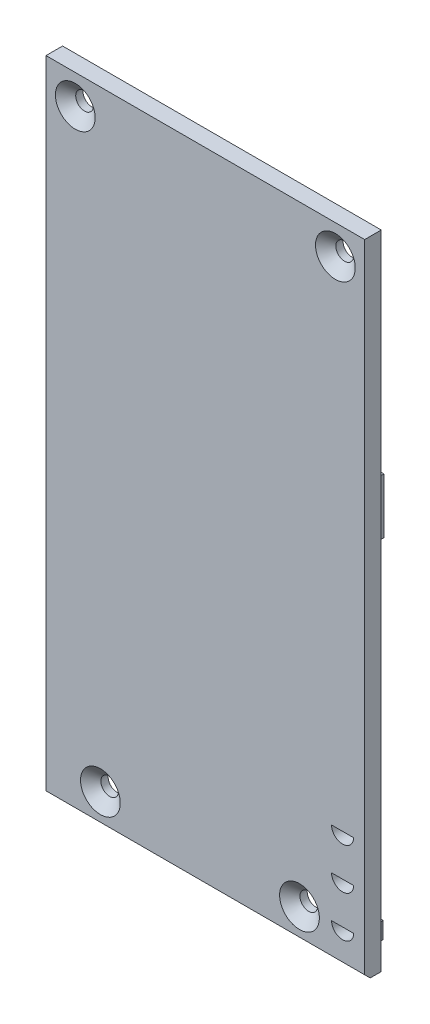
SolidWorks part; units mm, degrees
ref_plane "Front Plane" through (0, 0, 0) normal (0, 0, 1) x (1, 0, 0)
ref_plane "Top Plane" through (0, 0, 0) normal (0, 1, 0) x (1, 0, 0)
ref_plane "Right Plane" through (0, 0, 0) normal (1, 0, 0) x (0, 0, -1)
sketch "Sketch1" plane through (0, 0, 0) normal (0, 0, 1) x (1, 0, 0)
  line L1 (0, 0) -> (57.7, 0)
  line L2 (0, 0) -> (0, 114.7)
  line L3 (0, 114.7) -> (57.7, 114.7)
  line L4 (57.7, 0) -> (57.7, 114.7)
  dimension "D1" = 114.7
  dimension "D2" = 57.7
extrude "Boss-Extrude1" add sketch "Sketch1" along normal blind 3
sketch "Sketch2" plane through (0, 0, 3) normal (0, 0, 1) x (1, 0, 0)
  line L1 (0, 114.7) -> (0, 0) construction
  line L2 (57.7, 114.7) -> (0, 114.7) construction
  line L3 (57.7, 0) -> (57.7, 114.7) construction
  line L4 (0, 0) -> (57.7, 0) construction
  circle A0 centre (5.3, 109.4) radius 1.6
  circle A1 centre (52.4, 109.4) radius 1.6
  circle A2 centre (9.85, 4.2) radius 1.6
  circle A3 centre (45.9, 4.2) radius 1.6
  dimension "D1" = 3.2
  dimension "D2" = 5.3
  dimension "D3" = 5.3
  dimension "D4" = 5.3
  dimension "D5" = 5.3
  dimension "D6" = 9.85
  dimension "D7" = 11.8
  dimension "D8" = 4.2
  dimension "D9" = 4.2
extrude "Cut-Extrude1" cut sketch "Sketch2" against normal blind 3
chamfer "Chamfer1" distance 2 angle 40 4 edges at (11.45, 4.2, 3) (54, 109.4, 3) (6.9, 109.4, 3) (47.5, 4.2, 3)
sketch "Sketch4" plane through (0, 0, 0) normal (0, -1, 0) x (1, 0, 0)
  line L1 (0, 3) -> (57.7, 3)
  line L2 (0, 3) -> (0, 0)
  line L3 (0, 0) -> (57.7, 0)
  line L4 (57.7, 3) -> (57.7, 0)
extrude "Boss-Extrude2" add sketch "Sketch4" along normal blind 1.6
sketch "Sketch5" plane through (0, 0, 0) normal (0, 0, -1) x (-1, 0, 0)
  line L1 (-45.7, 105.2) -> (-26.7, 105.2)
  line L2 (-45.7, 105.2) -> (-45.7, 99.2)
  line L3 (-45.7, 99.2) -> (-26.7, 99.2)
  line L4 (-26.7, 105.2) -> (-26.7, 99.2)
  line L5 (-57.7, 114.7) -> (0, 114.7) construction
  line L6 (-57.7, -1.6) -> (-57.7, 114.7) construction
  line L7 (0, 114.7) -> (0, -1.6) construction
  dimension "D1" = 6
  dimension "D2" = 12
  dimension "D3" = 26.7
  dimension "D4" = 9.5
extrude "Boss-Extrude3" add sketch "Sketch5" along normal blind 2.2
sketch "Sketch7" plane through (0, 0, 0) normal (0, 0, -1) x (-1, 0, 0)
  line L0 (-45.7, 105.2) -> (-45.7, 99.2) construction
  line L1 (-45.7, 104.2) -> (-26.7, 104.2)
  line L2 (-45.7, 104.2) -> (-45.7, 107.2)
  line L3 (-45.7, 107.2) -> (-26.7, 107.2)
  line L4 (-26.7, 104.2) -> (-26.7, 107.2)
  line L5 (-57.7, 114.7) -> (0, 114.7) construction
  dimension "D1" = 3
  dimension "D2" = 7.5
extrude "Boss-Extrude4" add sketch "Sketch7" along normal blind 4.5
chamfer "Chamfer2" distance 0.5 angle 45 1 edges at (36.2, 104.2, -4.5)
sketch "Sketch8" plane through (0, 0, 0) normal (0, 0, -1) x (-1, 0, 0)
  line L0 (0, -1.6) -> (-57.7, -1.6) construction
  line L1 (-39.7, 29.4) -> (-14, 29.4)
  line L2 (-39.7, 29.4) -> (-39.7, 26.4)
  line L3 (-39.7, 26.4) -> (-14, 26.4)
  line L4 (-14, 29.4) -> (-14, 26.4)
  line L5 (0, 114.7) -> (0, -1.6) construction
  line L6 (-57.7, -1.6) -> (-57.7, 114.7) construction
  line L8 (-54.7, 31.4) -> (-29.7, 31.4)
  line L9 (-54.7, 31.4) -> (-54.7, 35.4)
  line L10 (-54.7, 35.4) -> (-29.7, 35.4)
  line L11 (-29.7, 31.4) -> (-29.7, 35.4)
  dimension "D1" = 3
  dimension "D2" = 28
  dimension "D3" = 14
  dimension "D4" = 18
  dimension "D5" = 4
  dimension "D6" = 2
  dimension "D7" = 3
  dimension "D8" = 25
extrude "Boss-Extrude5" add sketch "Sketch8" along normal blind 2
sketch "Sketch9" plane through (0, 0, 0) normal (0, 0, -1) x (-1, 0, 0)
  line L0 (-57.7, -1.6) -> (-57.7, 114.7) construction
  line L1 (-39.7, 17.4) -> (-14, 17.4)
  line L2 (-39.7, 17.4) -> (-39.7, 10.4)
  line L3 (-39.7, 10.4) -> (-14, 10.4)
  line L4 (-14, 17.4) -> (-14, 10.4)
  line L5 (0, 114.7) -> (0, -1.6) construction
  line L7 (0, -1.6) -> (-57.7, -1.6) construction
  dimension "D1" = 7
  dimension "D2" = 18
  dimension "D3" = 14
  dimension "D4" = 19
extrude "Boss-Extrude6" add sketch "Sketch9" along normal blind 4.5
sketch "Sketch10" plane through (0, 0, 3) normal (0, 0, 1) x (1, 0, 0)
  line L0 (53.7, -1.6) -> (53.7, 25.8665) construction
  line L1 (57.7, -1.6) -> (0, -1.6) construction
  line L2 (57.7, -1.6) -> (57.7, 114.7) construction
  circle A0 centre (53.7, 19.9) radius 2
  circle A1 centre (53.7, 12.4) radius 2
  circle A2 centre (53.7, 4.9) radius 2
  point P10 (53.6857, 25.8665)
  dimension "D1" = 21.5
  dimension "D2" = 14
  dimension "D3" = 6.5
  dimension "D4" = 4
extrude "Cut-Extrude2" cut sketch "Sketch10" against normal blind 3
sketch "Sketch11" plane through (0, 0, 3) normal (0, 0, 1) x (1, 0, 0)
  line L1 (51.7, 19.9) -> (55.7, 19.9)
  line L2 (51.7, 19.9) -> (51.7, 21.9)
  line L3 (51.7, 21.9) -> (55.7, 21.9)
  line L4 (55.7, 19.9) -> (55.7, 21.9)
  line L5 (51.7, 12.4) -> (55.7, 12.4)
  line L6 (51.7, 12.4) -> (51.7, 14.4)
  line L7 (51.7, 14.4) -> (55.7, 14.4)
  line L8 (55.7, 12.4) -> (55.7, 14.4)
  line L9 (51.7, 4.9) -> (55.7, 4.9)
  line L10 (51.7, 4.9) -> (51.7, 6.9)
  line L11 (51.7, 6.9) -> (55.7, 6.9)
  line L12 (55.7, 4.9) -> (55.7, 6.9)
  circle A0 centre (53.7, 19.9) radius 2 construction
  circle A1 centre (53.7, 12.4) radius 2 construction
  circle A2 centre (53.7, 4.9) radius 2 construction
extrude "Boss-Extrude7" add sketch "Sketch11" against normal blind 0.7
sketch "Sketch12" plane through (0, 0, 0) normal (0, 0, -1) x (-1, 0, 0)
  line L1 (-55.7, 19.9) -> (-51.7, 19.9)
  line L2 (-55.7, 19.9) -> (-55.7, 17.9061)
  line L3 (-55.7, 17.9061) -> (-51.7, 17.9061)
  line L4 (-51.7, 19.9) -> (-51.7, 17.9061)
  line L5 (-55.7, 12.4) -> (-51.7, 12.4)
  line L6 (-55.7, 12.4) -> (-55.7, 10.4)
  line L7 (-55.7, 10.4) -> (-51.7, 10.4)
  line L8 (-51.7, 12.4) -> (-51.7, 10.4)
  line L9 (-55.7, 4.9) -> (-51.7, 4.9)
  line L10 (-55.7, 4.9) -> (-55.7, 2.9)
  line L11 (-55.7, 2.9) -> (-51.7, 2.9)
  line L12 (-51.7, 4.9) -> (-51.7, 2.9)
  circle A0 centre (-53.7, 12.4) radius 2 construction
extrude "Boss-Extrude11" add sketch "Sketch12" against normal blind 0.7
sketch "Sketch13" plane through (0, 0, 0) normal (0, 0, -1) x (-1, 0, 0)
  line L0 (0, 114.7) -> (0, -1.6) construction
  line L1 (-56.05, 1.6) -> (-51.55, 1.6)
  line L2 (-56.05, 1.6) -> (-56.05, 4.6)
  line L3 (-56.05, 4.6) -> (-51.55, 4.6)
  line L4 (-51.55, 1.6) -> (-51.55, 4.6)
  line L5 (-5, 1.6) -> (-2, 1.6)
  line L6 (-5, 1.6) -> (-5, 4.6)
  line L7 (-5, 4.6) -> (-2, 4.6)
  line L8 (-2, 1.6) -> (-2, 4.6)
  line L9 (-57.7, -1.6) -> (-57.7, 114.7) construction
  line L10 (0, -1.6) -> (-57.7, -1.6) construction
  point P8 (-3.5, 4.6)
  point P11 (-53.8, 4.6)
  point P14 (-56.05, 3.1)
  point P17 (-2, 3.1)
  dimension "D1" = 4.5
  dimension "D2" = 3
  dimension "D3" = 3
  dimension "D4" = 3
  dimension "D5" = 3.5
  dimension "D6" = 3.9
  dimension "D7" = 4.7
  dimension "D8" = 4.7
extrude "Boss-Extrude12" add sketch "Sketch13" along normal blind 2
sketch "Sketch14" plane through (0, 0, 0) normal (0, 0, -1) x (-1, 0, 0)
  line L0 (-57.7, -1.6) -> (-57.7, 114.7) construction
  line L1 (-56.2, 74.7) -> (-53.7, 74.7)
  line L2 (-56.2, 74.7) -> (-56.2, 64.7)
  line L3 (-56.2, 64.7) -> (-53.7, 64.7)
  line L4 (-53.7, 74.7) -> (-53.7, 64.7)
  line L5 (-27.5, 74.7) -> (-25, 74.7)
  line L6 (-27.5, 74.7) -> (-27.5, 64.7)
  line L7 (-27.5, 64.7) -> (-25, 64.7)
  line L8 (-25, 74.7) -> (-25, 64.7)
  line L9 (0, 114.7) -> (0, -1.6) construction
  line L10 (-57.7, 114.7) -> (0, 114.7) construction
  dimension "D1" = 2.5
  dimension "D2" = 2.5
  dimension "D3" = 10
  dimension "D4" = 10
  dimension "D5" = 1.5
  dimension "D6" = 25
  dimension "D7" = 40
  dimension "D8" = 40
extrude "Boss-Extrude13" add sketch "Sketch14" along normal blind 2
chamfer "Chamfer3" distance 1 angle 45 1 edges at (28.85, -1.6, 3)
